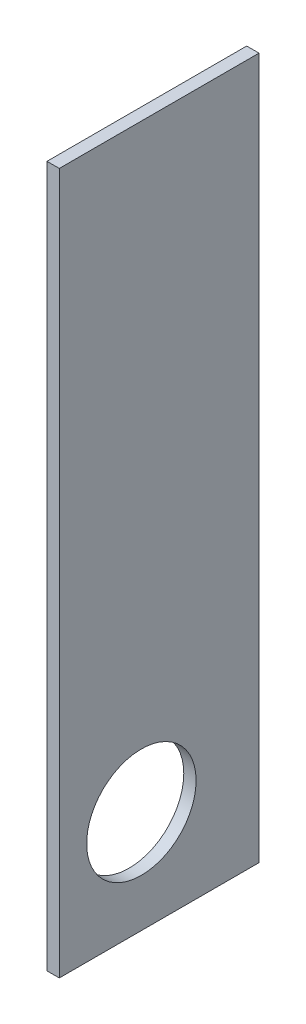
SolidWorks part; units mm, degrees
ref_plane "Front Plane" through (0, 0, 0) normal (0, 0, 1) x (1, 0, 0)
ref_plane "Top Plane" through (0, 0, 0) normal (0, 1, 0) x (1, 0, 0)
ref_plane "Right Plane" through (0, 0, 0) normal (1, 0, 0) x (0, 0, -1)
sketch "Sketch1" plane through (0, 0, 0) normal (1, 0, 0) x (0, 0, -1)
  line L1 (24.3921, -967.2196) -> (-267.6079, -967.2196)
  line L2 (24.3921, -967.2196) -> (24.3921, 57.7804)
  line L3 (24.3921, 57.7804) -> (-267.6079, 57.7804)
  line L4 (-267.6079, -967.2196) -> (-267.6079, -836.1219)
  line L5 (24.3921, -967.2196) -> (-267.6079, 57.7804) construction
  line L6 (24.3921, 57.7804) -> (-267.6079, -967.2196) construction
  line L7 (-267.6079, -676.1219) -> (-267.6079, 57.7804)
  line L10 (-267.6079, -676.1219) -> (-267.6079, -836.1219)
  circle A0 centre (-147.6079, -817.2196) radius 80
  point P0 (-121.6079, -454.7196)
  dimension "D3" = 160
  dimension "D4" = 120
  dimension "D1" = 292
  dimension "D2" = 1025
  dimension "D5" = 150
extrude "Boss-Extrude1" add sketch "Sketch1" along normal blind 18
equation "\"H_POLKI\"=1025"
equation "\"D2@Sketch1\"=\"H_POLKI\""
equation "\"DSP_WIDTH\"=18"
equation "\"D1@Boss-Extrude1\"=\"DSP_WIDTH\""
